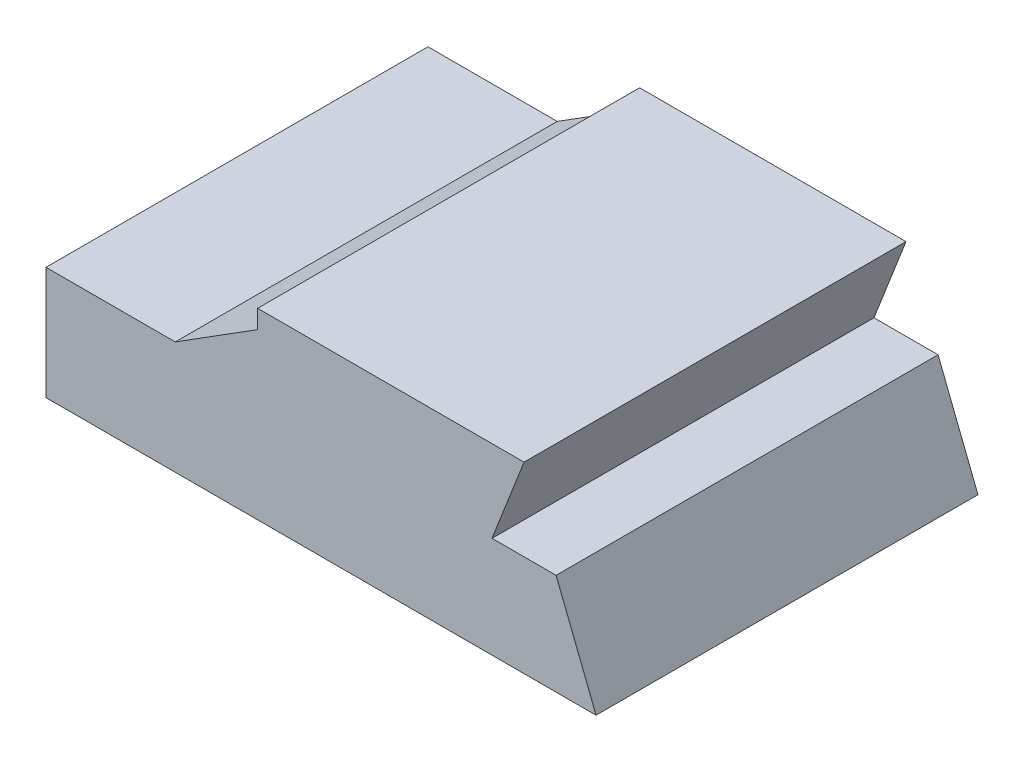
SolidWorks part; units mm, degrees
ref_plane "前视基准面" through (0, 0, 0) normal (0, 0, 1) x (1, 0, 0)
ref_plane "上视基准面" through (0, 0, 0) normal (0, 1, 0) x (1, 0, 0)
ref_plane "右视基准面" through (0, 0, 0) normal (1, 0, 0) x (0, 0, -1)
sketch "草图1" plane through (0, 0, 0) normal (0, 0, 1) x (1, 0, 0)
  line L1 (0, 29.5569) -> (33.8411, 29.5569)
  line L2 (116.7701, 26.4939) -> (125.1562, 47.9624)
  line L3 (152.6325, 126.9813) -> (90.1698, 135.4275)
  line L6 (89.0201, 126.9249) -> (126.841, 106.3205)
  line L8 (0, 0) -> (0, 29.5569)
  line L9 (33.8411, 29.5569) -> (55.4044, 43.1338)
  line L11 (144.001, 0) -> (133.5423, 26.4939)
  line L14 (89.661, -18.3061) -> (89.661, 35.0616) construction
  line L17 (125.1562, 47.9624) -> (140.6985, 47.9624)
  line L18 (140.6985, 47.9624) -> (157.4376, 120.0186)
  line L20 (133.5423, 26.4939) -> (116.7701, 26.4939)
  line L21 (55.4044, 43.1338) -> (55.4044, 95.8971)
  line L22 (0, 0) -> (144.001, 0)
  line L23 (55.4044, 95.8971) -> (92.2029, 95.8971)
  arc A2 (81.7861, 122.3112) -> (92.2029, 95.8971) centre (19.0918, 82.3258) cw
  arc A9 (90.1698, 135.4275) -> (81.7861, 122.3112) centre (89.0201, 126.9249) ccw
  arc A10 (157.4376, 120.0186) -> (152.6325, 126.9813) centre (151.866, 121.3129) ccw
  circle A15 centre (126.841, 106.3205) radius 27.6011
  dimension "D2" = 55.2022
  dimension "D3" = 74.36
  dimension "D4" = 8.58
  dimension "D5" = 5.72
  dimension "D1" = 106.3205
  dimension "D6" = 19.0918
  dimension "D7" = 33.8411
  dimension "D8" = 55.4044
  dimension "D9" = 81.7861
  dimension "D10" = 90.1698
  dimension "D11" = 89.661
  dimension "D12" = 151.866
  dimension "D13" = 92.2029
  dimension "D14" = 116.7701
  dimension "D15" = 125.1562
  dimension "D16" = 126.841
  dimension "D17" = 133.5423
  dimension "D18" = 140.6985
  dimension "D19" = 144.001
  dimension "D20" = 26.4939
  dimension "D21" = 29.5569
  dimension "D22" = 157.4376
  dimension "D23" = 43.1338
  dimension "D24" = 47.9624
extrude "凸台-拉伸1" add sketch "草图1" along normal mid plane 100
sketch "草图2" plane through (0, 0, 50) normal (0, 0, 1) x (1, 0, 0)
  line L0 (125.1562, 47.9624) -> (37.9215, 47.9624)
split "分割1" trim tools "草图2" bodies to split 106 resulting bodies 107 108
delete or keep bodies "实体-删除/保留 1" type delete bodies bodies 107
